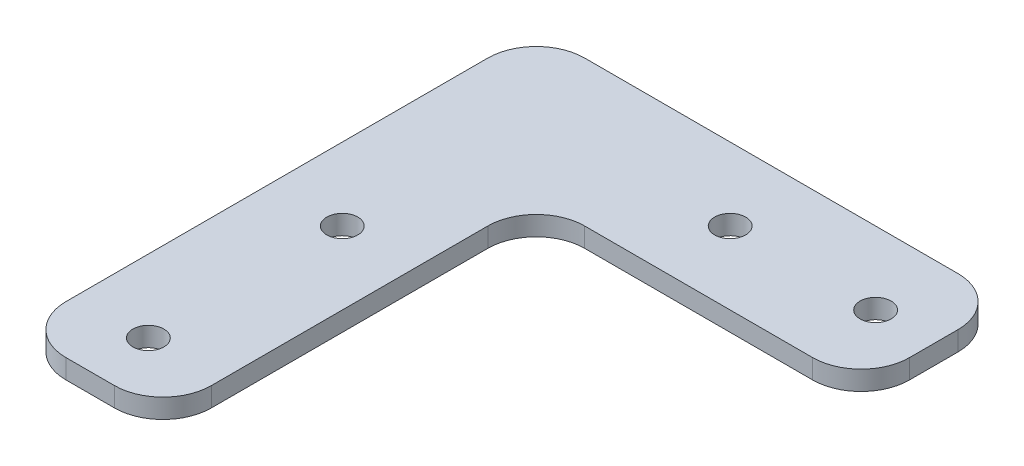
SolidWorks part; units mm, degrees
material "Carbon Fiber"
ref_plane "Front Plane" through (0, 0, 0) normal (0, 0, 1) x (1, 0, 0)
ref_plane "Top Plane" through (0, 0, 0) normal (0, 1, 0) x (1, 0, 0)
ref_plane "Right Plane" through (0, 0, 0) normal (1, 0, 0) x (0, 0, -1)
sketch "Sketch1" plane through (0, 0, 0) normal (0, 1, 0) x (1, 0, 0)
  line L0 (0, -40) -> (0, 0) construction
  line L1 (0, 0) -> (7.5, -7.5) construction
  line L2 (7.5, -7.5) -> (7.5, -46)
  line L3 (7.5, -46) -> (-7.5, -46)
  line L4 (-7.5, -46) -> (-7.5, 7.5)
  line L5 (41, 7.5) -> (-7.5, 7.5)
  line L6 (41, -7.5) -> (41, 7.5)
  line L7 (7.5, -7.5) -> (41, -7.5)
  circle A0 centre (0, -40) radius 1.6
  circle A1 centre (0, -20) radius 1.6
  circle A2 centre (20, 0) radius 1.6
  circle A3 centre (35, 0) radius 1.6
  dimension "D2" = 7.5
  dimension "D3" = 20
  dimension "D1" = 3.2
  dimension "D4" = 15
  dimension "D5" = 15
  dimension "D6" = 6
  dimension "D7" = 6
extrude "Boss-Extrude1" add sketch "Sketch1" along normal blind 2
fillet "Fillet1" radius 5 6 edges at (7.5, 1, 46) (-7.5, 1, 46) (-7.5, 1, -7.5) (41, 1, -7.5) (41, 1, 7.5) (7.5, 1, 7.5)
